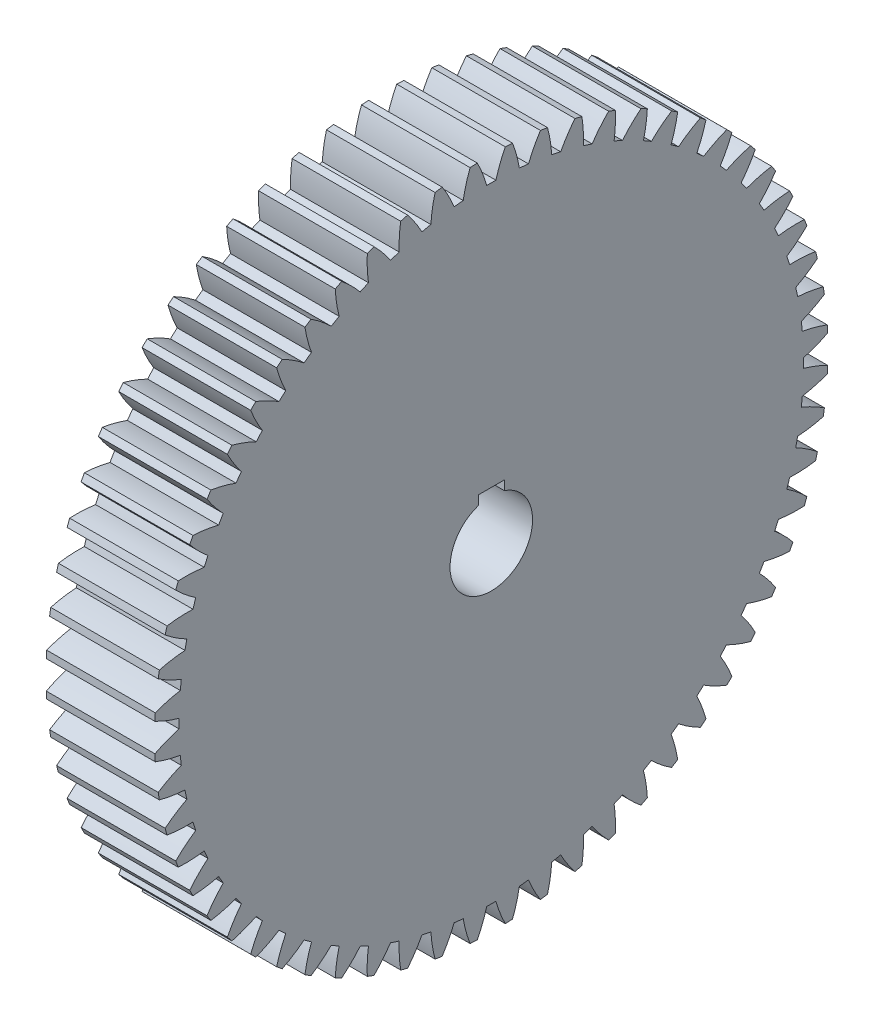
SolidWorks part; units mm, degrees
ref_plane "Plane1" through (0, 0, 0) normal (0, 0, 1) x (1, 0, 0)
ref_plane "Plane2" through (0, 0, 0) normal (0, 1, 0) x (1, 0, 0)
ref_plane "Plane3" through (0, 0, 0) normal (1, 0, 0) x (0, 0, -1)
sketch "HoldingSke" plane through (0, 0, 0) normal (0, 1, 0) x (1, 0, 0)
  line L0 (0, 0) -> (0.1, -0.1732)
  line L1 (-15, 0) -> (100, 0) construction
  line L2 (0, 0) -> (-2.1039, 2.3779)
  line L3 (0, 0) -> (-11.863, 4.5341)
  line L4 (0, 0) -> (4.318, 7.479)
  line L5 (0, 0) -> (-46.8476, -17.4728)
  line L6 (0, 0) -> (-41.4481, -27.9652)
  line L7 (-2.1039, 2.3779) -> (8.6586, 51.2059)
  line L8 (-76.2, 54.61) -> (-72.9, 54.61)
  line L9 (-71.009, 38.7566) -> (-53.1078, 45.2721)
  line L10 (-76.2, 71.12) -> (104.1128, 71.12)
  line L11 (0, 0) -> (-50, 0)
  line L12 (-76.2, 101.6) -> (-76.033, 101.6)
  line L13 (24.9733, 27.94) -> (52.9518, 28.4284)
  line L14 (24.9733, 27.94) -> (24.9743, 27.94)
  line L15 (24.9733, 27.94) -> (100.4006, 29.5858)
  line L16 (-63.627, -5) -> (-12.827, -5)
  circle A0 centre (0, 0) radius 19
  circle A1 centre (0, 0) radius 37.5
  circle A2 centre (0, 0) radius 37.5
  circle A3 centre (0, 0) radius 19
  dimension "MHD" = 75
  dimension "Hub_dia" = 75
  dimension "Bore" = 38
  dimension "MBD" = 38
  dimension "Num_teeth" = 60
  dimension "Pitch" = 0.2
  dimension "Overall_len" = 50
  dimension "Show_teeth" = 60
  dimension "Thickness" = 50
  dimension "OAL" = 50.0001
  dimension "T_dim" = 3.3
  dimension "Ap" = 20
  dimension "H" = 19.05
  dimension "Pitch_radius" = 180.3128
  dimension "Width" = 50
  dimension "Backlash" = 0.167
  dimension "Addendum_fac" = 1
  dimension "Dedendum_fac" = 1.25
  dimension "Clearance_fac" = 0.25
  dimension "Dedendum_add" = 0.001
  dimension "Module" = 5
sketch "BasProSke" plane through (0, 0, 0) normal (0, 1, 0) x (1, 0, 0)
  line L0 (-10, 0) -> (60, 0) construction
  line L1 (0, 0) -> (0, 155)
  line L2 (0, 0) -> (50, 0)
  line L3 (50, 0) -> (50, 155)
  line L4 (50, 155) -> (0, 155)
  dimension "Thickness" = 50
  dimension "Diameter" = 310
revolve "Base-Revolve" add sketch "BasProSke" angle 360 about L0
sketch "TooCutSke" plane through (0, 0, 0) normal (1, 0, 0) x (0, 0, -1)
  line L1 (0, 0) -> (0, 107) construction
  line L2 (0, 0) -> (-4.2188, 149.9407) construction
  line L3 (0, 0) -> (-15.6962, 299.5009) construction
  line L4 (-4.2188, 149.9407) -> (-7.8481, 149.7505) construction
  arc A0 (2.1133, 143.7335) -> (-2.1133, 143.7335) centre (0, 0) ccw
  arc A1 (6.4708, 154.8903) -> (-6.4708, 154.8903) centre (0, 0) ccw
  circle A2 centre (0, 0) radius 150 construction
  circle A3 centre (0, 0) radius 140.9539 construction
  arc A4 (-2.1133, 143.7335) -> (-6.4708, 154.8903) centre (-59.9014, 127.5924) ccw
  arc A5 (6.4708, 154.8903) -> (2.1133, 143.7335) centre (59.9014, 127.5924) ccw
  dimension "Root_dia" = 287.498
  dimension "Overcut_dia" = 310.0508
  dimension "Pitch_dia" = 300
  dimension "Base_dia" = 281.9078
  dimension "Flank_rad" = 60
  dimension "Half_ang" = 3
  dimension "Half_CT" = 3.6343
extrude "ToothCut" cut sketch "TooCutSke" along normal through all
fillet "Breaks" [suppressed] radius 0.1
fillet "RootFillets" [suppressed] radius 1.251
pattern_circular "TeethCuts" count 60 every 6 about axis through (-10, 0, 0) along (1, 0, 0) of "ToothCut", "RootFillets", "Breaks"
sketch "HubNeaOneSke" plane through (0, 0, 0) normal (-1, 0, 0) x (0, 0, 1)
  circle A0 centre (0, 0) radius 37.5
  dimension "Diameter" = 75
extrude "HubNearOne" [suppressed] add sketch "HubNeaOneSke" along normal blind 12.7001
sketch "HubNeaBotSke" plane through (0, 0, 0) normal (-1, 0, 0) x (0, 0, 1)
  circle A0 centre (0, 0) radius 37.5
  dimension "Diameter" = 75
extrude "HubNearBoth" [suppressed] add sketch "HubNeaBotSke" along normal blind 6.35
ref_plane "FarPln" through (50, 0, 0) normal (1, 0, 0) x (0, 0, -1)
sketch "HubFarSke" plane through (50, 0, 0) normal (1, 0, 0) x (0, 0, -1)
  circle A0 centre (0, 0) radius 37.5
  dimension "Diameter" = 75
extrude "HubFar" [suppressed] add sketch "HubFarSke" along normal blind 6.35
sketch "BorSke" plane through (0, 0, 0) normal (1, 0, 0) x (0, 0, -1)
  circle A0 centre (0, 0) radius 19
  dimension "Diameter" = 38
extrude "Bore" cut sketch "BorSke" along normal mid plane 100.0001
sketch "KeySke" plane through (0, 0, 0) normal (1, 0, 0) x (0, 0, -1)
  line L0 (-6, 0) -> (-6, 22.3)
  line L1 (-6, 22.3) -> (6, 22.3)
  line L2 (6, 22.3) -> (6, 0)
  line L3 (0, 0) -> (0, 34) construction
  line L4 (-6, 0) -> (6, 0)
  dimension "Offset" = 22.3
  dimension "Width" = 12
extrude "Keyway" cut sketch "KeySke" along normal mid plane 100.0001
pattern_circular "Keyway2" [suppressed] count 2 every 90 about axis through (-10, 0, 0) along (1, 0, 0)
ref_plane "Plane4" through (50, 22.3, -6) normal (0, 1, 0) x (1, 0, 0)
equation "' \"Module@HoldingSke\" = 6.35"
equation "' \"Num_teeth@HoldingSke\" = 12"
equation "' \"Ap@HoldingSke\" =  20"
equation "' \"Ap@HoldingSke\" = 20"
equation "' \"Width@HoldingSke\" = 0.5 * 25.4"
equation "' \"Hub_dia@HoldingSke\"= 1 * 25.4"
equation "' \"Hub_dia@HoldingSke\" = 1 * 25.4"
equation "' \"Overall_len@HoldingSke\" = 1.0 * 25.4"
equation "' \"Bore@HoldingSke\" = 0.75 * 25.4"
equation "' \"T_dim@HoldingSke\" = 0.1 * 25.4"
equation "' \"Width@KeySke\" = 0.25 * 25.4"
equation "' \"Show_teeth@HoldingSke\" = 13"
equation "' \"Backlash@HoldingSke\" = 0.009 * 25.4"
equation "' \"Addendum_fac@HoldingSke\" = 1.0"
equation "' \"Dedendum_fac@HoldingSke\" = 1.25"
equation "' \"Dedendum_add@HoldingSke\" = 0.00005 * 25.4"
equation "' \"Clearance_fac@HoldingSke\" = 0.25"
equation "\"Pitch@HoldingSke\" = 1 / \"Module@HoldingSke\""
equation "\"Overcut_dia@TooCutSke\" = (\"Num_teeth@HoldingSke\" + 2 * \"Addendum_fac@HoldingSke\") / \"Pitch@HoldingSke\" + 0.002 * 25.4"
equation "\"Pitch_dia@TooCutSke\" = \"Num_teeth@HoldingSke\" / \"Pitch@HoldingSke\""
equation "\"Base_dia@TooCutSke\" = \"Num_teeth@HoldingSke\" / \"Pitch@HoldingSke\" * cos((\"Ap@HoldingSke\"  * 3.14159265 / 180))"
equation "\"Root_dia@TooCutSke\" = (\"Num_teeth@HoldingSke\" + 2) / \"Pitch@HoldingSke\" - 2 * (\"Addendum_fac@HoldingSke\" + \"Dedendum_fac@HoldingSke\") / \"Pitch@HoldingSke\" - \"Dedendum_add@HoldingSke\" * 2"
equation "\"Half_ang@TooCutSke\" = 180 / \"Num_teeth@HoldingSke\""
equation "\"Half_CT@TooCutSke\" = \"Num_teeth@HoldingSke\" / \"Pitch@HoldingSke\" * sin((3.14159265 / 2 / \"Num_teeth@HoldingSke\")) / 2 - 7 * \"Backlash@HoldingSke\" / 4"
equation "\"Flank_rad@TooCutSke\" = \"Num_teeth@HoldingSke\" / \"Pitch@HoldingSke\" / 5"
equation "\"Radius@RootFillets\" = \"Clearance_fac@HoldingSke\" / \"Pitch@HoldingSke\" + \"Dedendum_add@HoldingSke\""
equation "\"Break_rad@Breaks\" = 0.02 / \"Pitch@HoldingSke\""
equation "\"Thickness@HoldingSke\" = \"Width@HoldingSke\""
equation "\"OAL@HoldingSke\" = \"Thickness@HoldingSke\""
equation "\"MHD@HoldingSke\" = (\"Num_teeth@HoldingSke\" + 2) / \"Pitch@HoldingSke\" - 2 * (\"Addendum_fac@HoldingSke\" + \"Dedendum_fac@HoldingSke\")  / \"Pitch@HoldingSke\" - \"Dedendum_add@HoldingSke\" * 2"
equation "\"MBD@HoldingSke\" = (\"Num_teeth@HoldingSke\" + 2) / \"Pitch@HoldingSke\" - 2 * (\"Addendum_fac@HoldingSke\" + \"Dedendum_fac@HoldingSke\")  / \"Pitch@HoldingSke\" - \"Dedendum_add@HoldingSke\" * 2 - 0.002 * 25.4"
equation "\"MHD@HoldingSke\" = ((sgn( \"MHD@HoldingSke\" - \"Hub_dia@HoldingSke\" )-1)*( \"MHD@HoldingSke\" - \"Hub_dia@HoldingSke\" ))/-2+ \"Hub_dia@HoldingSke\""
equation "\"MBD@HoldingSke\" = ((sgn( \"MBD@HoldingSke\" - \"Bore@HoldingSke\" )-1)*( \"MBD@HoldingSke\" - \"Bore@HoldingSke\" ))/-2+ \"Bore@HoldingSke\""
equation "\"OAL@HoldingSke\" = ((sgn( \"OAL@HoldingSke\" - \"Overall_len@HoldingSke\" )+1)*( \"OAL@HoldingSke\" - \"Overall_len@HoldingSke\" ))/2 + \"Overall_len@HoldingSke\" + 0.000002 * 25.4"
equation "\"Num_teeth@TeethCuts\" = int( \"Show_teeth@HoldingSke\" ) + 1"
equation "\"Num_teeth@TeethCuts\" = ((sgn( \"Num_teeth@TeethCuts\" - \"Num_teeth@HoldingSke\" )-1)*( \"Num_teeth@TeethCuts\" - \"Num_teeth@HoldingSke\" ))/-2+ \"Num_teeth@HoldingSke\""
equation "\"Num_teeth@TeethCuts\" = ((sgn( \"Num_teeth@TeethCuts\" - 2.0)+1)*( \"Num_teeth@TeethCuts\" - 2.0))/2 +2.0"
equation "\"Angle@TeethCuts\" = 360.0 / \"Num_teeth@HoldingSke\""
equation "\"Diameter@BasProSke\" = (\"Num_teeth@HoldingSke\" + 2 * \"Addendum_fac@HoldingSke\") / \"Pitch@HoldingSke\""
equation "\"Thickness@BasProSke\"  = \"Thickness@HoldingSke\""
equation "' \"Fillet_rad@BasProSke\" =  \"Thickness@HoldingSke\" * 0.05"
equation "' \"Fillet_rad@BasProSke\" = \"Thickness@HoldingSke\" * 0.05"
equation "\"MHD@HoldingSke\" = ((sgn( \"MHD@HoldingSke\" - \"Root_dia@TooCutSke\" )-1)*( \"MHD@HoldingSke\" - \"Root_dia@TooCutSke\" ))/-2+ \"Root_dia@TooCutSke\""
equation "\"Diameter@HubNeaOneSke\" = \"MHD@HoldingSke\""
equation "\"Length@HubNearOne\" = \"OAL@HoldingSke\" - \"Thickness@BasProSke\""
equation "\"Diameter@HubNeaBotSke\" = \"MHD@HoldingSke\""
equation "\"Length@HubNearBoth\" = ( \"OAL@HoldingSke\" - \"Thickness@BasProSke\" ) / 2.0"
equation "\"Thickness@FarPln\" = \"Thickness@BasProSke\""
equation "\"Diameter@HubFarSke\" = \"MHD@HoldingSke\""
equation "\"Length@HubFar\" = ( \"OAL@HoldingSke\" - \"Thickness@BasProSke\" ) / 2.0"
equation "\"Diameter@BorSke\" = \"MBD@HoldingSke\""
equation "\"D1@Bore\" = \"OAL@HoldingSke\" * 2.0"
equation "\"D1@Keyway\" = \"OAL@HoldingSke\" * 2.0"
equation "\"Offset@KeySke\" = \"T_dim@HoldingSke\" + \"MBD@HoldingSke\" / 2.0"
